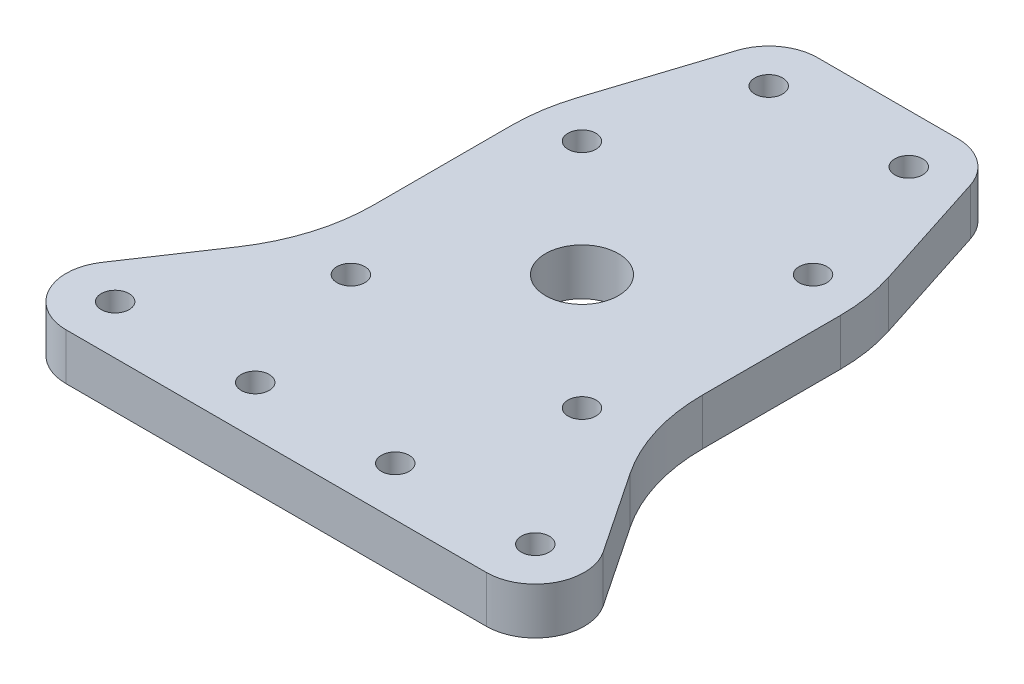
SolidWorks part; units mm, degrees
material "6061-T6 (SS)"
ref_plane "Front Plane" through (0, 0, 0) normal (0, 0, 1) x (1, 0, 0)
ref_plane "Top Plane" through (0, 0, 0) normal (0, 1, 0) x (1, 0, 0)
ref_plane "Right Plane" through (0, 0, 0) normal (1, 0, 0) x (0, 0, -1)
sketch "Sketch1" plane through (0, 0, 0) normal (0, 1, 0) x (1, 0, 0)
  line L0 (-57.15, 0) -> (0, 114.3)
  line L1 (0, 114.3) -> (57.15, 0)
  line L2 (0, 114.3) -> (0, 0) construction
  line L3 (-57.15, 0) -> (57.15, 0)
  line L4 (-31.75, 3.175) -> (-31.75, 15.875) construction
  line L5 (6.35, 3.175) -> (31.75, 3.175) construction
  line L6 (6.35, 3.175) -> (6.35, 15.875) construction
  line L7 (6.35, 15.875) -> (31.75, 15.875) construction
  line L8 (31.75, 3.175) -> (31.75, 15.875) construction
  line L9 (-12.7, 73.025) -> (12.7, 73.025) construction
  line L10 (-12.7, 73.025) -> (-12.7, 85.725) construction
  line L11 (-12.7, 85.725) -> (12.7, 85.725) construction
  line L12 (12.7, 73.025) -> (12.7, 85.725) construction
  line L13 (-6.35, 15.875) -> (-31.75, 15.875) construction
  line L14 (-6.35, 3.175) -> (-6.35, 15.875) construction
  line L15 (-6.35, 3.175) -> (-31.75, 3.175) construction
  point P0 (0, 0)
  dimension "D3" = 12.7
  dimension "D1" = 114.3
  dimension "D2" = 114.3
  dimension "D4" = 25.4
  dimension "D5" = 57.15
  dimension "D6" = 3.175
  dimension "D7" = 12.7
extrude "Boss-Extrude1" add sketch "Sketch1" against normal blind 6.35
hole_wizard "#6 Clearance Hole1" positions "Sketch3" profile "Sketch2" hole size "#6" standard "ANSI Inch" end condition through all
sketch "Sketch3" plane through (0, 0, 0) normal (0, 1, 0) x (1, 0, 0)
  line L0 (-12.7, 85.725) -> (12.7, 85.725) construction
  line L1 (-12.7, 73.025) -> (-12.7, 85.725) construction
  line L2 (-12.7, 73.025) -> (12.7, 73.025) construction
  line L3 (12.7, 73.025) -> (12.7, 85.725) construction
  line L4 (6.35, 15.875) -> (31.75, 15.875) construction
  line L5 (6.35, 3.175) -> (6.35, 15.875) construction
  line L6 (6.35, 3.175) -> (31.75, 3.175) construction
  line L7 (31.75, 3.175) -> (31.75, 15.875) construction
  line L8 (-12.7, 85.725) -> (12.7, 85.725) construction
  line L9 (-12.7, 73.025) -> (-12.7, 85.725) construction
  line L10 (-12.7, 73.025) -> (12.7, 73.025) construction
  line L11 (12.7, 73.025) -> (12.7, 85.725) construction
  line L12 (6.35, 15.875) -> (31.75, 15.875) construction
  line L13 (6.35, 3.175) -> (6.35, 15.875) construction
  line L14 (6.35, 3.175) -> (31.75, 3.175) construction
  line L15 (31.75, 3.175) -> (31.75, 15.875) construction
  line L16 (0, 0) -> (0, 114.3) construction
  line L17 (-57.15, 0) -> (57.15, 0) construction
  line L20 (19.05, 15.875) -> (19.05, 3.175) construction
  line L21 (9.525, 9.525) -> (28.575, 9.525) construction
  line L23 (-9.525, 79.375) -> (9.525, 79.375) construction
  point P32 (28.575, 9.525)
  point P34 (9.525, 9.525)
  point P37 (-9.525, 79.375)
  point P39 (9.525, 79.375)
  point P53 (-28.575, 9.525)
  point P54 (-9.525, 9.525)
  dimension "D1" = 19.05
sketch "Sketch2" plane through (28.575, 0, -9.525) normal (1, 0, 0) x (0, 0, 1)
  line L0 (0, 0) -> (0, 6.35)
  line L1 (0, 6.35) -> (1.8986, 6.35)
  line L2 (1.8986, 6.35) -> (1.8986, 0)
  line L5 (1.8986, 0) -> (0, 0)
  line L11 (0, -6.35) -> (0, 107.95) construction
  dimension "Thru Hole Dia." = 3.7973
  dimension "Thru Hole Depth" = 6.35
fillet "Fillet1" radius 17.78 3 edges at (0, -3.175, -114.3) (57.15, -3.175, 0) (-57.15, -3.175, 0)
hole_wizard "7/16-20 Tapped Hole1" positions "Sketch6" profile "Sketch5" tap size "7/16-20" standard "ANSI Inch" end condition through all
sketch "Sketch6" plane through (0, 0, 0) normal (0, 1, 0) x (1, 0, 0)
  circle A0 centre (-9.525, 9.525) radius 1.8986 construction
  point P0 (0, 44.45)
  dimension "D1" = 34.925
sketch "Sketch5" plane through (0, 0, -44.45) normal (1, 0, 0) x (0, 0, 1)
  line L0 (0, 0) -> (0, 6.35)
  line L1 (0, 6.35) -> (4.9606, 6.35)
  line L2 (4.9606, 6.35) -> (4.9606, 0)
  line L5 (4.9606, 0) -> (0, 0)
  line L11 (0, -6.35) -> (0, 107.95) construction
  dimension "Thread Major Dia." = 9.9212
  dimension "Thru Tap Drill Depth" = 6.35
hole_wizard "#6 Clearance Hole2" positions "Sketch8" profile "Sketch7" hole size "#6" standard "ANSI Inch" end condition up to next
sketch "Sketch8" plane through (0, 0, 0) normal (0, 1, 0) x (1, 0, 0)
  line L0 (15.7154, 60.1654) -> (0, 44.45) construction
  line L2 (-15.7154, 60.1654) -> (0, 44.45) construction
  line L4 (0, 44.45) -> (0, 76.1788) construction
  circle A0 centre (0, 44.45) radius 22.225
  point P5 (-15.7154, 60.1654)
  point P7 (15.7154, 28.7346)
  point P9 (-15.7154, 28.7346)
  point P11 (15.7154, 60.1654)
  dimension "D1" = 44.45
  dimension "D2" = 90
  dimension "D3" = 45
sketch "Sketch7" plane through (-15.7154, 0, -60.1654) normal (1, 0, 0) x (0, 0, 1)
  line L0 (0, 0) -> (0, 6.35)
  line L1 (0, 6.35) -> (1.8986, 6.35)
  line L2 (1.8986, 6.35) -> (1.8986, 0)
  line L5 (1.8986, 0) -> (0, 0)
  line L11 (0, -6.35) -> (0, 107.95) construction
  dimension "Thru Hole Dia." = 3.7973
  dimension "Thru Hole Depth" = 6.35
sketch "Sketch9" plane through (0, 0, 0) normal (0, 1, 0) x (1, 0, 0)
  line L0 (-22.3766, 61.2122) -> (-22.3766, 28.7346)
  line L1 (22.3766, 61.2122) -> (22.3766, 28.7346)
  line L2 (-15.7154, 66.8266) -> (15.7154, 66.8266)
  line L3 (-15.7154, 22.0734) -> (15.7154, 22.0734)
  line L4 (-28.575, 2.8639) -> (28.575, 2.8639)
  line L5 (-9.525, 86.0361) -> (9.525, 86.0361)
  line L6 (-21.2508, 32.4401) -> (-34.1103, 13.2305)
  line L7 (0, 0) -> (0, 35.8505) construction
  line L8 (-28.3814, 0) -> (28.3814, 0) construction
  line L9 (21.2508, 32.4401) -> (34.1103, 13.2305)
  line L10 (-21.2508, 32.4401) -> (-34.1103, 13.2305)
  line L11 (-15.8651, 81.4181) -> (-22.3766, 61.2122)
  line L12 (15.8651, 81.4181) -> (22.3766, 61.2122)
  circle A0 centre (-28.575, 9.525) radius 6.6611
  circle A1 centre (-9.525, 9.525) radius 6.6611
  circle A2 centre (9.525, 9.525) radius 6.6611
  circle A3 centre (28.575, 9.525) radius 6.6611
  circle A4 centre (15.7154, 28.7346) radius 6.6611
  circle A5 centre (-15.7154, 28.7346) radius 6.6611
  circle A6 centre (-15.7154, 60.1654) radius 6.6611
  circle A7 centre (15.7154, 60.1654) radius 6.6611
  circle A8 centre (-9.525, 79.375) radius 6.6611
  circle A9 centre (9.525, 79.375) radius 6.6611
  circle A11 centre (-28.575, 9.525) radius 1.8986 construction
  dimension "D1" = 4.7625
extrude "Cut-Extrude1" cut sketch "Sketch9" against normal through all
fillet "Fillet2" radius 25.4 4 edges at (-22.3766, -3.175, -61.2122) (22.3766, -3.175, -61.2122) (22.3766, -3.175, -30.7583) (-22.3766, -3.175, -30.7583)
